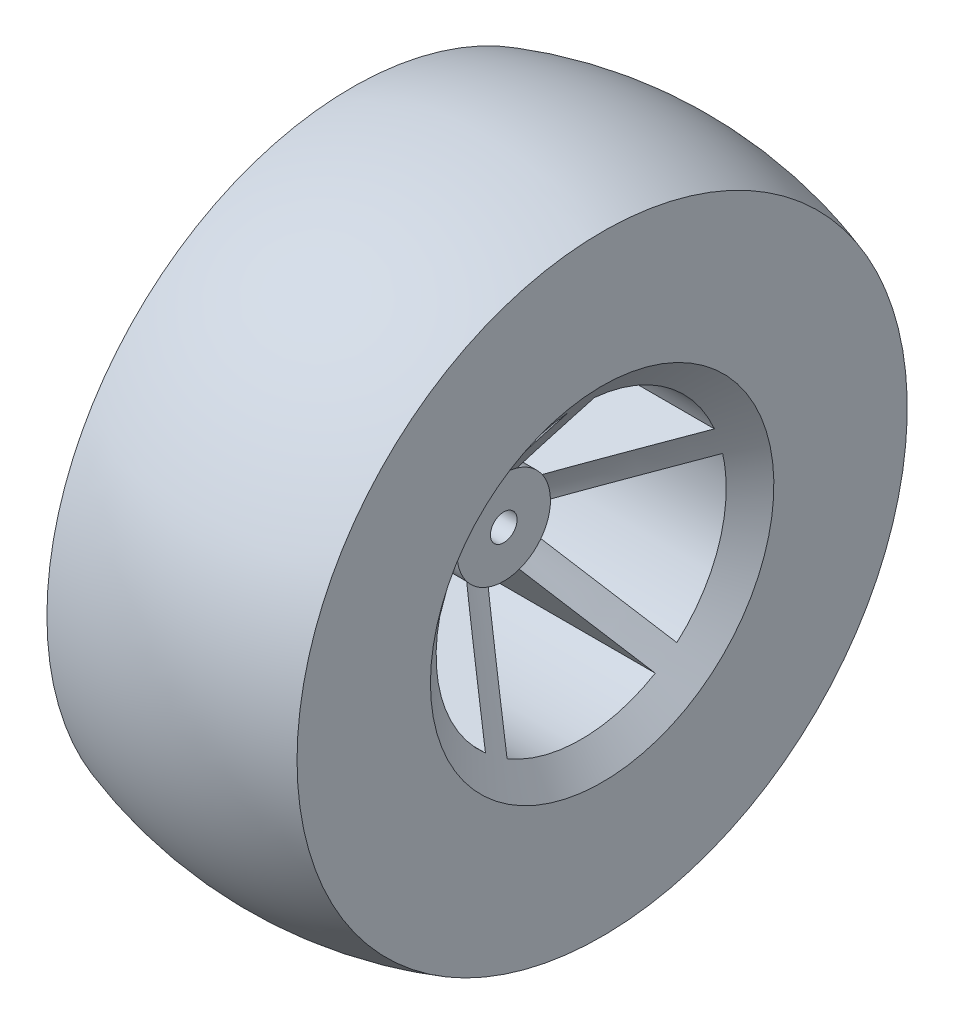
SolidWorks part; units mm, degrees
ref_plane "Front Plane" through (0, 0, 0) normal (0, 0, 1) x (1, 0, 0)
ref_plane "Top Plane" through (0, 0, 0) normal (0, 1, 0) x (1, 0, 0)
ref_plane "Right Plane" through (0, 0, 0) normal (1, 0, 0) x (0, 0, -1)
sketch "Sketch1" plane through (0, 0, 0) normal (0, 1, 0) x (1, 0, 0)
  line L0 (0, -48.75) -> (-98.1265, -48.75) construction
  line L1 (18.75, -45.7451) -> (18.75, -25.7451)
  line L2 (18.75, -25.7451) -> (4, -7)
  line L3 (4, -7) -> (4, -2)
  line L5 (0, -2) -> (0, -48.75)
  line L6 (4, -2) -> (0, -2)
  line L7 (-21.5213, 0) -> (29.4065, 0) construction
  arc A0 (18.75, -45.7451) -> (0, -48.75) centre (0, 11.25) cw
  dimension "D4" = 60
  dimension "D1" = 18.75
  dimension "D2" = 20
  dimension "D3" = 48.75
  dimension "D5" = 5
  dimension "D6" = 4
  dimension "D7" = 2
revolve "Revolve1" add sketch "Sketch1" angle 360 about L7
mirror "Mirror1" about plane through (0, 0, 2) normal (-1, 0, 0) of bodies 101
sketch "Sketch2" plane through (0, 0, 0) normal (1, 0, 0) x (0, 0, -1)
  line L0 (0, 0) -> (0, 21.7451)
  line L1 (0, 0) -> (20.6808, 6.7196)
  line L2 (0, 0) -> (12.7814, -17.5921)
  line L3 (0, 0) -> (-12.7814, -17.5921)
  line L4 (0, 0) -> (-20.6808, 6.7196)
  line L5 (2, 21.6529) -> (2, 2.7528)
  line L6 (2, 2.7528) -> (19.9751, 8.5932)
  line L7 (-2, 21.6529) -> (-2, 2.7528)
  line L8 (-2, 2.7528) -> (-19.9751, 8.5932)
  line L9 (-21.2112, 4.789) -> (-3.2361, -1.0515)
  line L10 (-3.2361, -1.0515) -> (-14.3453, -16.342)
  line L11 (-11.1092, -18.6931) -> (0, -3.4026)
  line L12 (0, -3.4026) -> (11.1092, -18.6931)
  line L13 (14.3453, -16.342) -> (3.2361, -1.0515)
  line L14 (3.2361, -1.0515) -> (21.2112, 4.789)
  circle A0 centre (0, 0) radius 21.7451
  circle A1 centre (0, 0) radius 7
  circle A2 centre (0, 0) radius 7 construction
  circle A3 centre (0, 0) radius 25.7451 construction
  dimension "D1" = 4
  dimension "D2" = 72
  dimension "D3" = 72
  dimension "D4" = 72
  dimension "D5" = 72
  dimension "D6" = 4
extrude "Cut-Extrude1" cut sketch "Sketch2" against normal through all both and the other way through all contours A1 L7 A0 L8 | A1 L6 A0 L5 | A1 L9 A0 L10 | A1 L13 A0 L14 | A1 L11 A0 L12
sketch "Sketch3" plane through (0, 0, 0) normal (1, 0, 0) x (0, 0, -1)
  circle A0 centre (0, 0) radius 48.75
  dimension "D1" = 97.5
